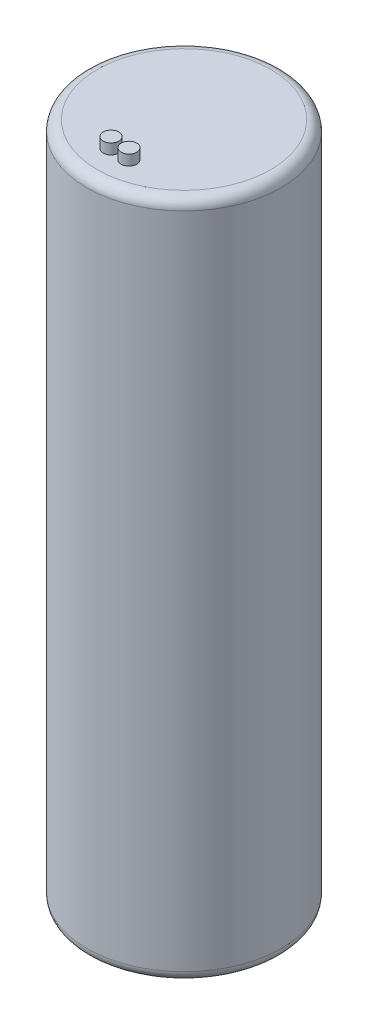
SolidWorks part; units mm, degrees
ref_plane "Front Plane" through (0, 0, 0) normal (0, 0, 1) x (1, 0, 0)
ref_plane "Top Plane" through (0, 0, 0) normal (0, 1, 0) x (1, 0, 0)
ref_plane "Right Plane" through (0, 0, 0) normal (1, 0, 0) x (0, 0, -1)
sketch "Sketch1" plane through (0, 0, 0) normal (0, 1, 0) x (1, 0, 0)
  circle A0 centre (0, 0) radius 9.3
  dimension "D1" = 18.6
extrude "Boss-Extrude1" add sketch "Sketch1" along normal blind 65
fillet "Fillet1" radius 1 2 edges at (0, 65, 9.3) (0, 0, 9.3)
sketch "Sketch2" plane through (0, 65, 0) normal (0, 1, 0) x (1, 0, 0)
  line L0 (0.694, -5.9597) -> (0, 0) construction
  line L1 (0, 0) -> (-1.0891, -5.9003) construction
  circle A0 centre (-1.0891, -5.9003) radius 0.75
  circle A1 centre (0.694, -5.9597) radius 0.75
  point P4 (0.694, -5.9003)
  dimension "D1" = 1.5
  dimension "D2" = 6
extrude "Boss-Extrude2" add sketch "Sketch2" along normal blind 1
